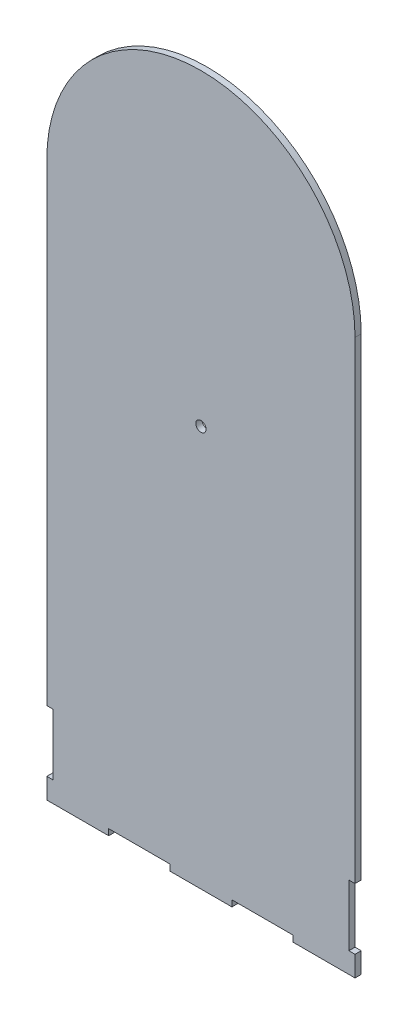
SolidWorks part; units mm, degrees
ref_plane "Front Plane" through (0, 0, 0) normal (0, 0, 1) x (1, 0, 0)
ref_plane "Top Plane" through (0, 0, 0) normal (0, 1, 0) x (1, 0, 0)
ref_plane "Right Plane" through (0, 0, 0) normal (1, 0, 0) x (0, 0, -1)
sketch "Sketch1" plane through (0, 0, 0) normal (0, 0, 1) x (1, 0, 0)
  line L0 (90.1, 0) -> (90.1, 3)
  line L1 (0, 0) -> (150, 0)
  line L2 (0, 0) -> (0, 270)
  line L3 (0, 270) -> (150, 270)
  line L4 (150, 0) -> (150, 270)
  line L5 (150, 39.8) -> (147, 39.8)
  line L6 (150, 39.8) -> (150, 10)
  line L7 (150, 10) -> (147, 10)
  line L8 (147, 39.8) -> (147, 10)
  line L9 (30.1, 0) -> (59.9, 0)
  line L10 (30.1, 0) -> (30.1, 3)
  line L11 (30.1, 3) -> (59.9, 3)
  line L12 (59.9, 0) -> (59.9, 3)
  line L13 (90.1, 0) -> (119.9, 0)
  line L14 (119.9, 0) -> (119.9, 3)
  line L15 (90.1, 3) -> (119.9, 3)
  line L16 (75, -730) -> (75, 49270) construction
  line L17 (0, 10) -> (3, 10)
  line L18 (3, 39.8) -> (3, 10)
  line L19 (0, 39.8) -> (3, 39.8)
  line L20 (0, 39.8) -> (0, 10)
  circle A0 centre (75, 270) radius 75
  circle A1 centre (75, 195) radius 2.5
  dimension "D11" = 5
  dimension "D1" = 270
  dimension "D2" = 150
  dimension "D3" = 3
  dimension "D4" = 10
  dimension "D5" = 29.8
  dimension "D6" = 3
  dimension "D7" = 29.8
  dimension "D8" = 30.1
  dimension "D10" = 30.2
  dimension "D9" = 2
extrude "Boss-Extrude1" add sketch "Sketch1" along normal blind 3 contours L1 L16 A0 L2 L19 L18 L17 L10 L11 L12 | L16 L1 L0 L15 L14 L4 L7 L8 L5 A0 | L16 L3 A0 | L16 A0 L3 | A0 L16 L3 | L3 L16 A0
